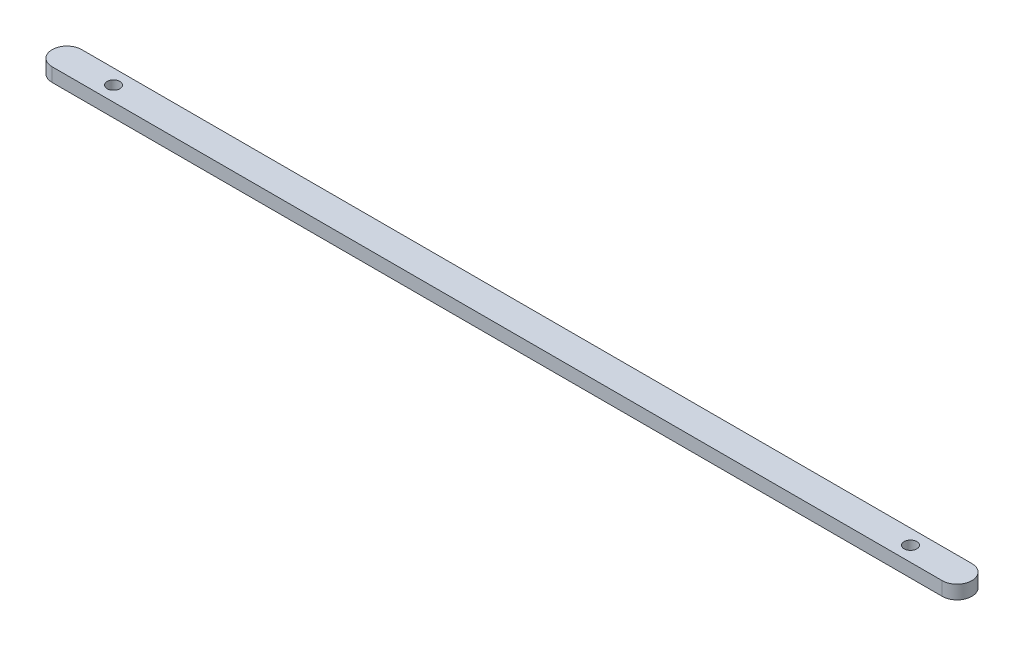
SolidWorks part; units mm, degrees
ref_plane "Front Plane" through (0, 0, 0) normal (0, 0, 1) x (1, 0, 0)
ref_plane "Top Plane" through (0, 0, 0) normal (0, 1, 0) x (1, 0, 0)
ref_plane "Right Plane" through (0, 0, 0) normal (1, 0, 0) x (0, 0, -1)
sketch "Sketch1" plane through (0, 0, 0) normal (0, 1, 0) x (1, 0, 0)
  line L0 (-105.08, 0) -> (105.08, 0) construction
  line L1 (-105.08, 3.5) -> (105.08, 3.5)
  line L2 (-105.08, -3.5) -> (105.08, -3.5)
  line L3 (0, -55) -> (0, 55) construction
  arc A0 (-105.08, 3.5) -> (-105.08, -3.5) centre (-105.08, 0) ccw
  arc A1 (105.08, -3.5) -> (105.08, 3.5) centre (105.08, 0) ccw
  circle A2 centre (-94.08, 0) radius 1.5
  circle A3 centre (94.08, 0) radius 1.5
  point P2 (0, 0)
  point P14 (0, 0)
  point P15 (-94.08, 0)
  dimension "D1" = 3.5
  dimension "D2" = 3
  dimension "D3" = 11
  dimension "D4" = 188.16
extrude "Boss-Extrude2" add sketch "Sketch1" along normal mid plane 3.22
